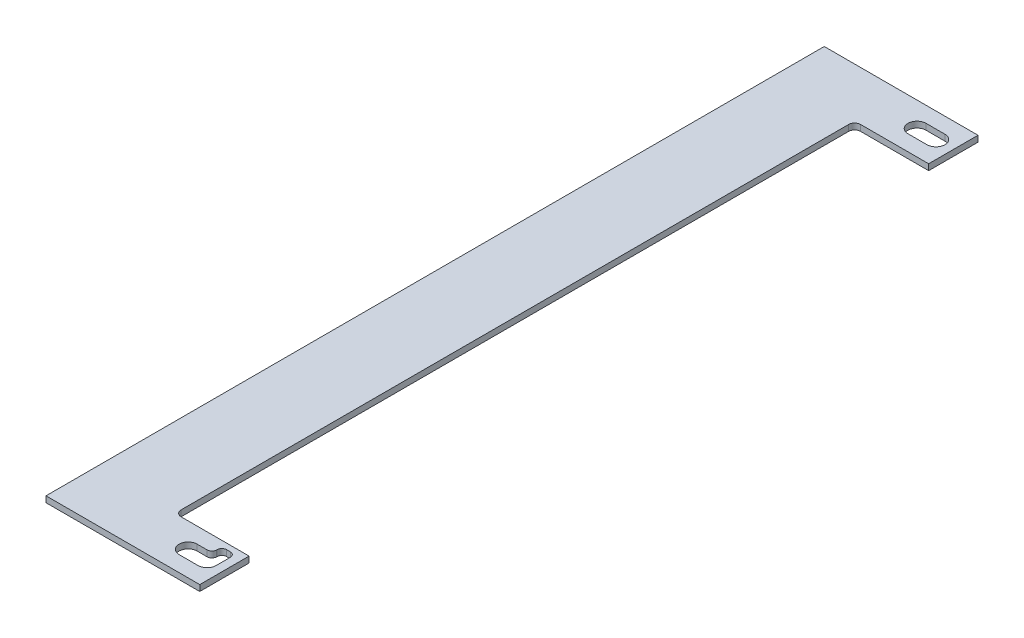
SolidWorks part; units mm, degrees
ref_plane "Front" through (0, 0, 0) normal (0, 0, 1) x (1, 0, 0)
ref_plane "Top" through (0, 0, 0) normal (0, 1, 0) x (1, 0, 0)
ref_plane "Right" through (0, 0, 0) normal (1, 0, 0) x (0, 0, -1)
sketch "Sketch1" plane through (0, 0, 0) normal (0, 1, 0) x (1, 0, 0)
  line L1 (-69.865, 256.2998) -> (11.135, 256.2998)
  line L2 (-69.865, 256.2998) -> (-69.865, -153.7002)
  line L3 (-69.865, -153.7002) -> (11.135, -153.7002)
  line L4 (11.135, 256.2998) -> (11.135, 248.0622)
  line L8 (11.135, 230.2997) -> (-27.865, 230.2997)
  line L9 (-27.865, 230.2997) -> (-27.865, -127.7002)
  line L10 (-27.865, -127.7002) -> (11.135, -127.7002)
  line L11 (11.135, -127.7002) -> (11.135, -145.4627)
  line L12 (2, 0) -> (2, 442.5145) construction
  line L13 (0, 0) -> (0, 41.3112) construction
  line L14 (2, 248.0623) -> (11.135, 248.0622) construction
  line L15 (11.135, 248.0622) -> (11.135, 238.5372)
  line L16 (11.135, 238.5372) -> (11.135, 230.2997)
  line L17 (-8, -135.9377) -> (2, -135.9377)
  line L18 (-8, -145.4627) -> (2, -145.4627)
  line L19 (11.135, -145.4627) -> (11.135, -153.7002)
  line L20 (2, 243.2998) -> (-39.9059, 243.2998) construction
  line L21 (-8, 248.0623) -> (2, 248.0623)
  line L22 (-8, 238.5373) -> (2, 238.5373)
  line L23 (-8, 243.2998) -> (-8, 266.1948) construction
  line L24 (2, -140.7002) -> (-24.7245, -140.7002) construction
  line L25 (0, 0) -> (-14.9283, 0) construction
  arc A0 (2, 248.0623) -> (2, 238.5373) centre (2, 243.2998) ccw construction
  arc A1 (4.7956, -136.8446) -> (6.5001, -142.2592) centre (2, -140.7002) ccw construction
  arc A2 (2, -145.4627) -> (2, -135.9377) centre (2, -140.7002) ccw
  arc A3 (2, 238.5373) -> (2, 248.0623) centre (2, 243.2998) ccw
  arc A4 (-8, 248.0623) -> (-8, 238.5373) centre (-8, 243.2998) ccw
  arc A5 (-8, -135.9377) -> (-8, -145.4627) centre (-8, -140.7002) ccw
  dimension "D3" = 9.525
  dimension "D1" = 26
  dimension "D2" = 42
  dimension "D4" = 13
  dimension "D5" = 13
  dimension "D6" = 2
  dimension "D7" = 26
  dimension "D8" = 10
  dimension "D9" = 153.7002
  dimension "D10" = 410
  dimension "D11" = 11.135
  dimension "D12" = 81
extrude "Extrude1" add sketch "Sketch1" along normal blind 3.175
sketch "Sketch2" plane through (0, 3.175, 0) normal (0, 1, 0) x (1, 0, 0)
  line L0 (-0.2375, -135.9377) -> (-0.2375, -130.7002)
  line L1 (2, -135.9377) -> (-8, -135.9377) construction
  line L2 (-0.2375, -130.7002) -> (6.7625, -130.7002)
  line L3 (6.7625, -130.7002) -> (6.7625, -140.7002)
  line L4 (2, -135.9377) -> (-0.2375, -135.9377)
  arc A0 (2, -145.4627) -> (2, -135.9377) centre (2, -140.7002) ccw construction
  arc A1 (6.7625, -140.7002) -> (2, -135.9377) centre (2, -140.7002) ccw
  dimension "D1" = 10
  dimension "D2" = 7
extrude "Cut-Extrude2" cut sketch "Sketch2" against normal through all
fillet "Fillet1" radius 2.5 3 edges at (6.7625, 1.5875, 130.7002) (-0.2375, 1.5875, 130.7002) (-0.2375, 1.5875, 135.9377)
fillet "Fillet2" radius 3.175 2 edges at (-27.865, 1.5875, 127.7002) (-27.865, 1.5875, -230.2997)
